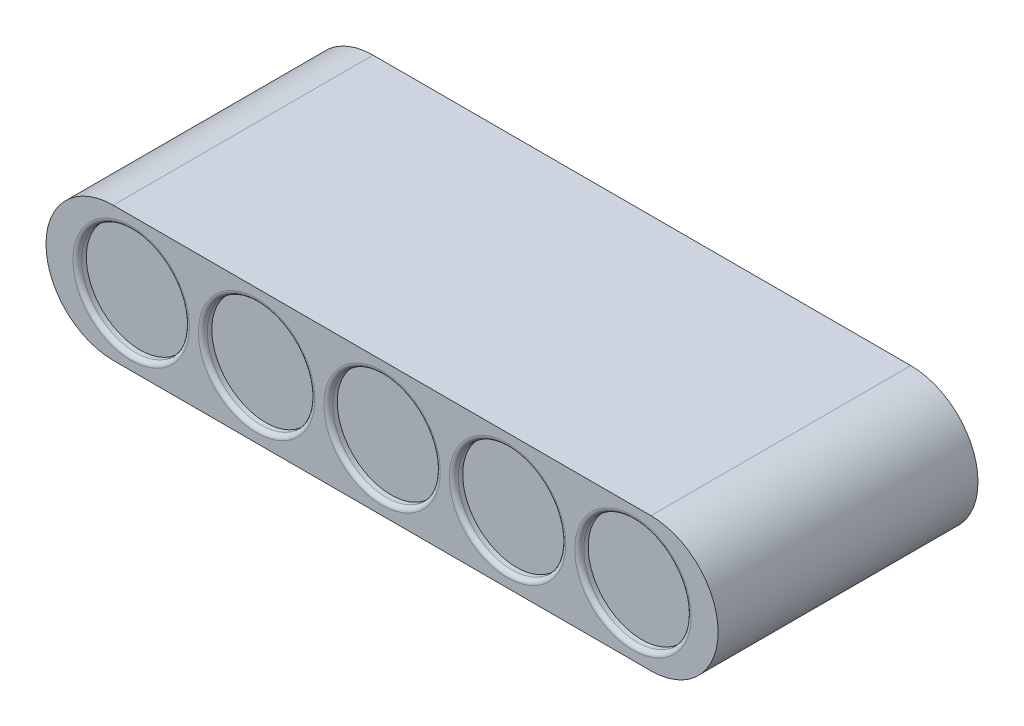
SolidWorks part; units mm, degrees
ref_plane "前视基准面" through (0, 0, 0) normal (0, 0, 1) x (1, 0, 0)
ref_plane "上视基准面" through (0, 0, 0) normal (0, 1, 0) x (1, 0, 0)
ref_plane "右视基准面" through (0, 0, 0) normal (1, 0, 0) x (0, 0, -1)
other "Configuration Table"
sketch "Sketch1" plane through (0, 0, 0) normal (0, 0, 1) x (1, 0, 0)
  line L0 (0, 15) -> (120, 15)
  line L1 (0, -15) -> (120, -15)
  line L2 (60, -15) -> (60, 15) construction
  circle A0 centre (0, 0) radius 15
  circle A1 centre (120, 0) radius 15
  dimension "D1" = 30
  dimension "D2" = 120
extrude "Boss-Extrude1" add sketch "Sketch1" along normal blind 58 contours A0 | L1 L2 L0 A0 | L2 L1 A1 L0 | A1 L0
sketch "Sketch2" plane through (0, 0, 58) normal (0, 0, 1) x (1, 0, 0)
  line L0 (0, 15) -> (120, 15) construction
  line L1 (0, -15) -> (120, -15) construction
  circle A0 centre (60, 0) radius 12
  circle A1 centre (88, 0) radius 12
  circle A2 centre (116, 0) radius 12
  circle A3 centre (32, 0) radius 12
  circle A4 centre (4, 0) radius 12
  point P7 (60, -15)
  dimension "D1" = 24
  dimension "D5" = 28
  dimension "D6" = 28
  dimension "D2" = 15
  dimension "D3" = 3
  dimension "D4" = 3
extrude "Cut-Extrude1" cut sketch "Sketch2" against normal blind 2
fillet "Fillet1" radius 1 5 edges at (128, 0, 58) (100, 0, 58) (72, 0, 58) (44, 0, 58) (16, 0, 58)
